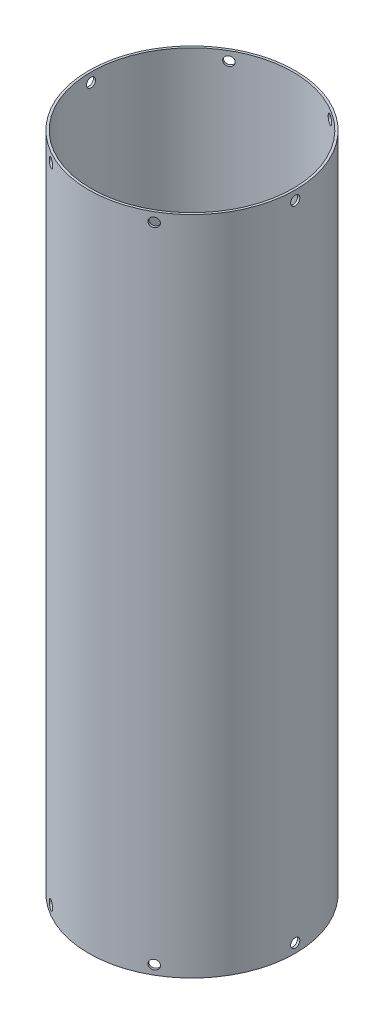
SolidWorks part; units mm, degrees
material "Hexcel AS4C (3000 Filaments)"
ref_plane "Front Plane" through (0, 0, 0) normal (0, 0, 1) x (1, 0, 0)
ref_plane "Top Plane" through (0, 0, 0) normal (0, 1, 0) x (1, 0, 0)
ref_plane "Right Plane" through (0, 0, 0) normal (1, 0, 0) x (0, 0, -1)
sketch "Sketch1" plane through (0, 0, 0) normal (0, 1, 0) x (1, 0, 0)
  circle A0 centre (0, 0) radius 139.7
  circle A1 centre (0, 0) radius 142.875
  dimension "D1" = 279.4
  dimension "D2" = 3.175
extrude "Boss-Extrude1" add sketch "Sketch1" along normal blind 914.4
ref_plane "Plane1" through (142.875, 0, 0) normal (1, 0, 0) x (0, 0, -1)
hole_wizard "1/2 (0.5) Diameter Hole1" positions "Sketch2" profile "Sketch3" hole size "1/2" standard "ANSI Inch"
sketch "Sketch2" plane through (142.875, 0, 0) normal (1, 0, 0) x (0, 0, -1)
  line L0 (0, 157.1625) -> (0, -157.1625) construction
  line L1 (142.875, 914.4) -> (-142.875, 914.4) construction
  point P0 (0, 901.7)
  dimension "D1" = 12.7
sketch "Sketch3" plane through (142.875, 901.7, 0) normal (0, 1, 0) x (0, 0, -1)
  line L0 (0, 0) -> (0, 333.7101)
  line L1 (0, 333.7101) -> (6.35, 333.7101)
  line L2 (6.35, 333.7101) -> (6.35, 0)
  line L5 (6.35, 0) -> (0, 0)
  line L11 (0, -6.35) -> (0, 107.95) construction
  dimension "Thru Hole Dia." = 12.7
  dimension "Thru Hole Depth" = 333.7101
pattern_circular "CirPattern1" count 6 over 360 about axis through (0, 914.4, 0) along (0, 1, 0) of "1/2 (0.5) Diameter Hole1"
ref_plane "Plane2" through (0, 457.2, 0) normal (0, 1, 0) x (1, 0, 0)
mirror "Mirror1" about plane through (0, 457.2, 0) normal (0, 1, 0) of "CirPattern1", "1/2 (0.5) Diameter Hole1"
